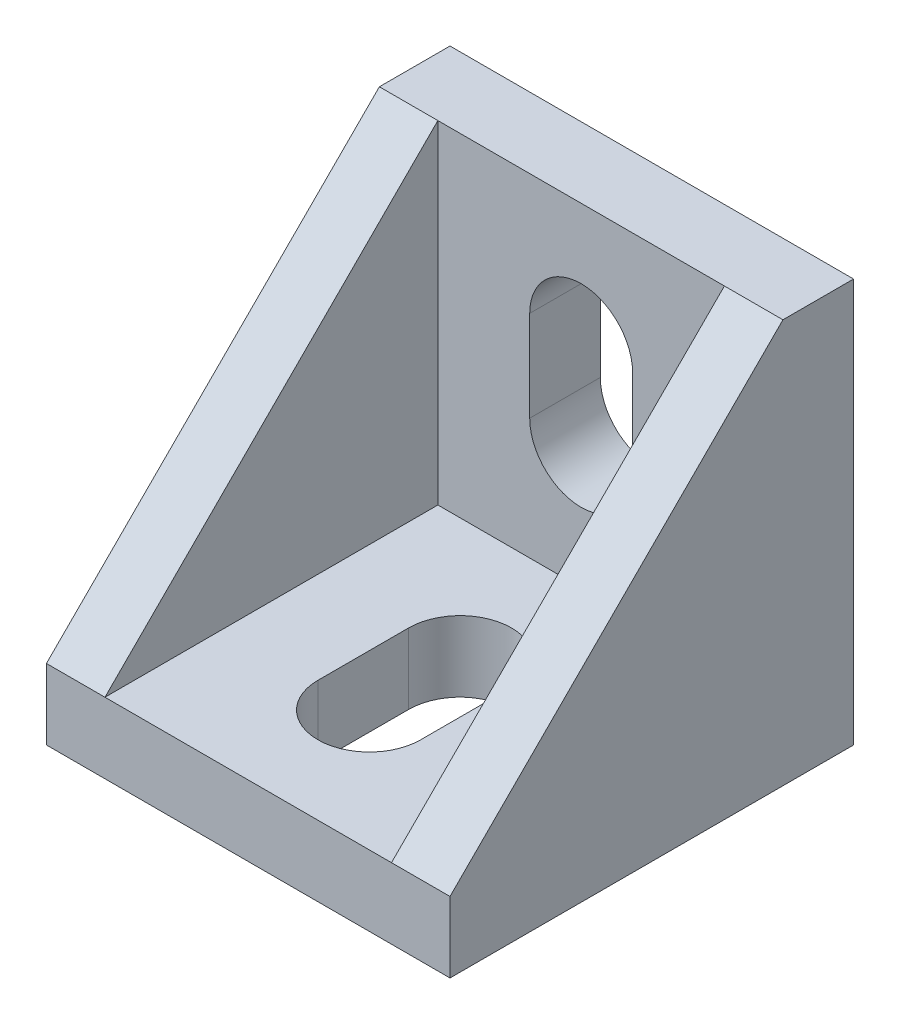
SolidWorks part; units mm, degrees
ref_plane "Front Plane" through (0, 0, 0) normal (0, 0, 1) x (1, 0, 0)
ref_plane "Top Plane" through (0, 0, 0) normal (0, 1, 0) x (1, 0, 0)
ref_plane "Right Plane" through (0, 0, 0) normal (1, 0, 0) x (0, 0, -1)
sketch "Sketch1" plane through (0, 0, 0) normal (0, 0, 1) x (1, 0, 0)
  line L1 (0, 0) -> (20, 0)
  line L2 (0, 0) -> (0, 20)
  line L3 (0, 20) -> (20, 20)
  line L4 (20, 0) -> (20, 20)
  dimension "D1" = 20
  dimension "D2" = 20
extrude "Extrude1" add sketch "Sketch1" along normal blind 3.5
sketch "Sketch2" plane through (0, 0, 3.5) normal (0, 0, 1) x (1, 0, 0)
  line L0 (20, 0) -> (20, 20) construction
  line L1 (0, 0) -> (20, 0)
  line L2 (0, 0) -> (0, 3.5)
  line L3 (0, 3.5) -> (20, 3.5)
  line L4 (20, 0) -> (20, 3.5)
  dimension "D1" = 3.5
extrude "Extrude2" add sketch "Sketch2" along normal blind 16.5
sketch "Sketch5" plane through (20, 0, 0) normal (1, 0, 0) x (0, 0, -1)
  line L0 (-3.5, 20) -> (-20, 3.5)
  line L1 (-20, 3.5) -> (-3.5, 3.5)
  line L2 (-3.5, 3.5) -> (-3.5, 20)
extrude "Extrude3" add sketch "Sketch5" against normal blind 2.9
sketch "Sketch6" plane through (0, 0, 0) normal (-1, 0, 0) x (0, 0, 1)
  line L0 (3.5, 20) -> (20, 3.5)
  line L1 (20, 3.5) -> (3.5, 3.5)
  line L2 (3.5, 3.5) -> (3.5, 20)
extrude "Extrude4" add sketch "Sketch6" against normal blind 2.9
sketch "Sketch7" plane through (0, 3.5, 0) normal (0, 1, 0) x (1, 0, 0)
  line L0 (10, -3.5) -> (10, -20) construction
  line L1 (17.1, -3.5) -> (2.9, -3.5) construction
  line L2 (17.1, -20) -> (2.9, -20) construction
  line L3 (7.45, -14) -> (7.45, -9.5)
  line L4 (12.55, -9.5) -> (12.55, -14)
  line L5 (7.45, -11.75) -> (12.55, -11.75) construction
  arc A0 (7.45, -9.5) -> (12.55, -9.5) centre (10, -9.5) cw
  arc A1 (7.45, -14) -> (12.55, -14) centre (10, -14) ccw
  dimension "D1" = 2.55
  dimension "D2" = 6
  dimension "D3" = 6
extrude "Cut-Extrude1" cut sketch "Sketch7" against normal up to next
sketch "Sketch8" plane through (0, 0, 3.5) normal (0, 0, 1) x (-1, 0, 0)
  line L0 (-10, -3.5) -> (-10, -20) construction
  line L3 (-12.55, -14) -> (-12.55, -9.5)
  line L4 (-7.45, -9.5) -> (-7.45, -14)
  line L5 (-12.55, -11.75) -> (-7.45, -11.75) construction
  line L6 (-17.1, -20) -> (-2.9, -20) construction
  line L7 (-17.1, -3.5) -> (-2.9, -3.5) construction
  arc A0 (-12.55, -9.5) -> (-7.45, -9.5) centre (-10, -9.5) cw
  arc A1 (-12.55, -14) -> (-7.45, -14) centre (-10, -14) ccw
  dimension "D1" = 2.55
  dimension "D2" = 6
  dimension "D3" = 6
extrude "Cut-Extrude2" cut sketch "Sketch8" against normal up to next
